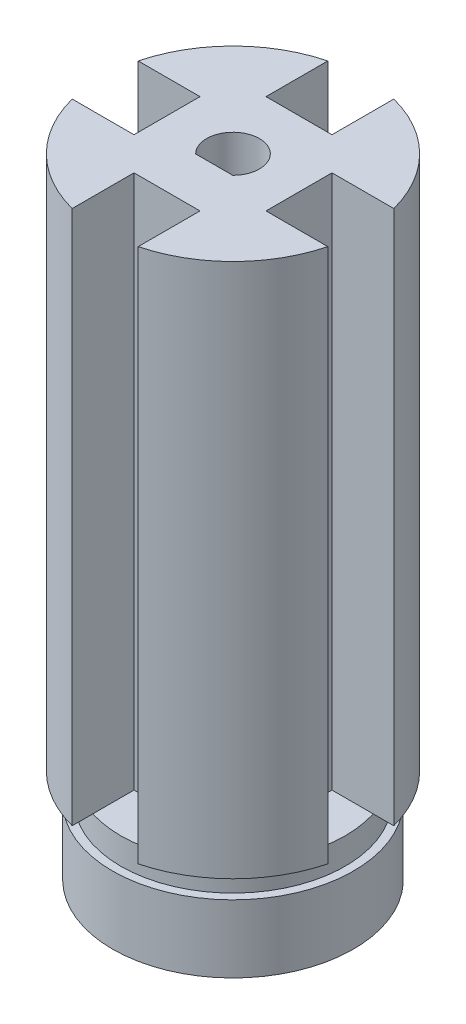
SolidWorks part; units mm, degrees
ref_plane "Front Plane" through (0, 0, 0) normal (0, 0, 1) x (1, 0, 0)
ref_plane "Top Plane" through (0, 0, 0) normal (0, 1, 0) x (1, 0, 0)
ref_plane "Right Plane" through (0, 0, 0) normal (1, 0, 0) x (0, 0, -1)
sketch "Sketch13" plane through (0, 0, 0) normal (0, 1, 0) x (1, 0, 0)
  circle A2 centre (0, 0) radius 18.25
  circle A3 centre (0, 0) radius 17
  dimension "D2" = 34
  dimension "D1" = 36.5
extrude "Boss-Extrude8" add sketch "Sketch13" along normal blind 0.255 and the other way blind 10
sketch "Sketch14" plane through (0, 0.255, 0) normal (0, 1, 0) x (1, 0, 0)
  line L0 (0, 0) -> (0, 3.425)
  line L1 (-2.0662, 3.425) -> (2.0662, 3.425)
  circle A0 centre (0, 0) radius 18.25
  circle A1 centre (0, 0) radius 4
  circle M2 centre (0, 0) radius 17
  dimension "D1" = 3.425
extrude "Boss-Extrude17" add sketch "Sketch14" along normal blind 5 contours A1 M2 | L1 A1
sketch "Sketch21" plane through (0, 5.255, 0) normal (0, 1, 0) x (1, 0, 0)
  circle A0 centre (0, 0) radius 20
  dimension "D1" = 40
extrude "Connector Cylinder" add sketch "Sketch21" along normal blind 80 and the other way blind 1
sketch "Sketch22" plane through (0, 85.255, 0) normal (0, 1, 0) x (1, 0, 0)
  line L0 (10, -5) -> (10, 5)
  line L4 (10, -5) -> (19.3649, -5)
  line L21 (-5, 19.3649) -> (-5, 10)
  line L39 (10, 5) -> (19.3649, 5)
  line L47 (-5, -10) -> (5, -10)
  line L51 (-10, -5) -> (-19.3649, -5)
  line L53 (-10, 5) -> (-19.3649, 5)
  line L54 (-10, 5) -> (-19.3649, 5)
  line L55 (-5, -10) -> (-5, -19.3649)
  line L58 (5, -10) -> (5, -19.3649)
  line L59 (-10, -5) -> (-10, 5)
  line L60 (-5, -10) -> (5, -10)
  line L64 (5, 19.3649) -> (5, 10)
  line L65 (-5, 10) -> (5, 10)
  line L67 (-10, 5) -> (-10, -5)
  circle A0 centre (0, 0) radius 20 construction
  circle M5 centre (0, 0) radius 20
  dimension "D1" = 10
  dimension "D2" = 10
  dimension "D3" = 9.3649
  dimension "D4" = 9.3649
  dimension "D5" = 10
  dimension "D6" = 9.3649
  dimension "D7" = 10
  dimension "D8" = 9.3649
sketch "Sketch23" plane through (0, 85.255, 0) normal (0, 1, 0) x (1, 0, 0)
  circle A0 centre (0, 0) radius 4
  dimension "D1" = 8
extrude "Cut-Extrude4" cut sketch "Sketch23" against normal blind 96.3
extrude "Connector Cylinder Cut" cut sketch "Sketch22" against normal blind 81 contours L58 L47 L55 M5 | L51 L59 L53 M5 | L21 L65 L64 M5 | L39 L0 L4 M5
sketch "Sketch25" plane through (0, 0.255, 0) normal (0, -1, 0) x (1, 0, 0)
  line L0 (-2.8067, 2.85) -> (2.8067, 2.85)
  circle A0 centre (0, 0) radius 4
  circle M3 centre (0, 0) radius 4
  dimension "D1" = 8
  dimension "D2" = 2.85
extrude "Key Cut" add sketch "Sketch25" against normal blind 85 contours L0 M3
